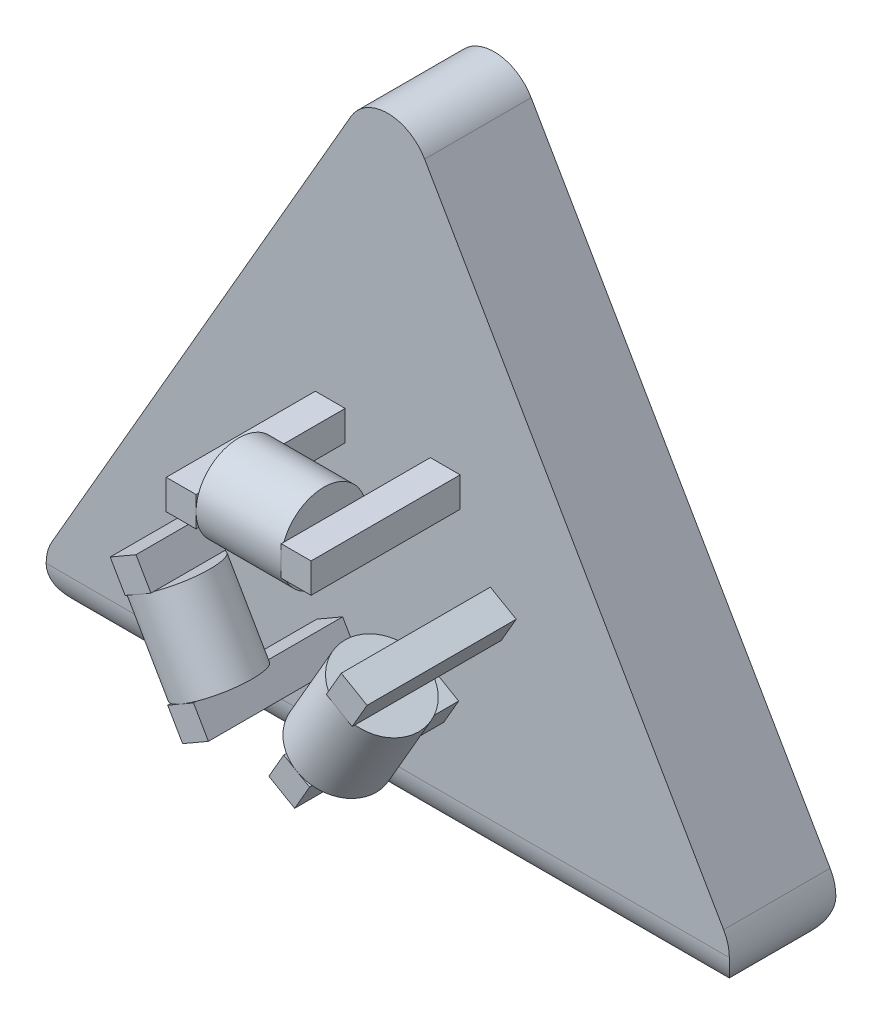
SolidWorks part; units mm, degrees
ref_plane "前视基准面" through (0, 0, 0) normal (0, 0, 1) x (1, 0, 0)
ref_plane "上视基准面" through (0, 0, 0) normal (0, 1, 0) x (1, 0, 0)
ref_plane "右视基准面" through (0, 0, 0) normal (1, 0, 0) x (0, 0, -1)
sketch "草图1" plane through (0, 0, 0) normal (0, 0, 1) x (1, 0, 0)
  line L0 (0, 0) -> (0, 40)
  line L1 (0, 40) -> (35, -20.6218)
  line L2 (0, 40) -> (-35, -20.6218)
  line L3 (-35, -20.6218) -> (35, -20.6218)
extrude "凸台-拉伸1" add sketch "草图1" along normal blind 10
fillet "圆角1" radius 4 5 edges at (0, -20.6218, 10) (0, -20.6218, 0) (35, -20.6218, 5) (-35, -20.6218, 5) (0, 40, 5)
sketch "草图2" plane through (0, 0, 10) normal (0, 0, 1) x (1, 0, 0)
  line L0 (0, 0) -> (0, 10)
  line L1 (0, 10) -> (4, 10)
  line L2 (0, 10) -> (-4, 10)
  line L3 (4, 10) -> (6.8, 10)
  line L4 (4, 10) -> (4, 7.2)
  line L5 (4, 7.2) -> (6.8, 7.2)
  line L6 (6.8, 10) -> (6.8, 7.2)
  line L7 (0, 0) -> (-8.6603, -5)
  line L8 (-4, 10) -> (-6.8, 10)
  line L9 (-4, 10) -> (-4, 7.2)
  line L10 (-4, 7.2) -> (-6.8, 7.2)
  line L11 (-6.8, 10) -> (-6.8, 7.2)
  line L12 (-8.6603, -5) -> (-10.6603, -1.5359)
  line L13 (-8.6603, -5) -> (-6.6603, -8.4641)
  line L14 (-10.6603, -1.5359) -> (-12.0603, 0.889)
  line L15 (-10.6603, -1.5359) -> (-8.2354, -0.1359)
  line L16 (-8.2354, -0.1359) -> (-9.6354, 2.289)
  line L17 (-12.0603, 0.889) -> (-9.6354, 2.289)
  line L18 (-6.6603, -8.4641) -> (-5.2603, -10.889)
  line L19 (-6.6603, -8.4641) -> (-4.2354, -7.0641)
  line L20 (-4.2354, -7.0641) -> (-2.8354, -9.489)
  line L21 (-5.2603, -10.889) -> (-2.8354, -9.489)
  line L22 (0, 0) -> (8.6603, -5)
  line L23 (8.6603, -5) -> (6.6603, -8.4641)
  line L24 (8.6603, -5) -> (10.6603, -1.5359)
  line L25 (6.6603, -8.4641) -> (5.2603, -10.889)
  line L26 (6.6603, -8.4641) -> (4.2354, -7.0641)
  line L27 (4.2354, -7.0641) -> (2.8354, -9.489)
  line L28 (5.2603, -10.889) -> (2.8354, -9.489)
  line L29 (10.6603, -1.5359) -> (12.0603, 0.889)
  line L30 (10.6603, -1.5359) -> (8.2354, -0.1359)
  line L31 (8.2354, -0.1359) -> (9.6354, 2.289)
  line L32 (12.0603, 0.889) -> (9.6354, 2.289)
extrude "凸台-拉伸2" add sketch "草图2" along normal blind 14 contours L8 L11 L10 L9 | L6 L3 L4 L5 | L29 L32 L31 L30 | L28 L25 L26 L27 | L18 L21 L20 L19 | L17 L14 L15 L16
sketch "草图3" plane through (-2, 3.4641, 0) normal (0.5, -0.866, 0) x (-0.866, -0.5, 0)
  line L0 (8.6, -24) -> (8.6, -20.4)
  line L1 (10, -24) -> (7.2, -24) construction
  circle A0 centre (8.6, -20.4) radius 3.6
extrude "凸台-拉伸3" add sketch "草图3" along normal blind 8
sketch "草图4" plane through (-4, 0, 0) normal (1, 0, 0) x (0, 0, -1)
  line L0 (-24, 8.6) -> (-20, 8.6)
  line L1 (-24, 10) -> (-24, 7.2) construction
  circle A0 centre (-20, 8.6) radius 4
extrude "凸台-拉伸4" add sketch "草图4" along normal blind 8
sketch "草图5" plane through (2, 3.4641, 0) normal (-0.5, -0.866, 0) x (-0.866, 0.5, 0)
  line L0 (-8.6, -24) -> (-8.6, -20)
  line L1 (-10, -24) -> (-7.2, -24) construction
  circle A0 centre (-8.6, -20) radius 4
extrude "凸台-拉伸5" add sketch "草图5" along normal blind 8
sketch "草图6" plane through (0, 0, 0) normal (0, 0, -1) x (-1, 0, 0)
  line L0 (0, 0) -> (0, -2)
  line L1 (0, -2) -> (0, 10)
  line L2 (-10, -3) -> (10, -3)
  line L3 (-10, -3) -> (-10, -1)
  line L4 (-10, -1) -> (10, -1)
  line L5 (10, -3) -> (10, -1)
  line L6 (-10, -3) -> (10, -1) construction
  line L7 (-10, -1) -> (10, -3) construction
  line L8 (0, 10) -> (7.5, 10)
  line L9 (0, 10) -> (-7.5, 10)
  circle A0 centre (7.5, 10) radius 2
  circle A1 centre (-7.5, 10) radius 2
extrude "切除-拉伸1" cut sketch "草图6" against normal blind 8
hole_wizard "M4 螺纹孔1" positions "草图11" profile "草图10" tap size "M4" standard "GB"
sketch "草图11" plane through (0, 0, 0) normal (0, 0, -1) x (-1, 0, 0)
  point P0 (-7.4974, 10.0202)
  point P2 (7.5604, 10.0202)
sketch "草图10" plane through (7.4974, 10.0202, 0) normal (1, 0, 0) x (0, 1, 0)
  line L0 (0, 0) -> (0, 5.9914)
  line L1 (0, 5.9914) -> (1.65, 5)
  line L2 (1.65, 5) -> (1.65, 0)
  line L5 (1.65, 0) -> (0, 0)
  line L10 (0, 5.9914) -> (-1.65, 5) construction
  line L11 (0, -6.35) -> (0, 107.95) construction
  dimension "螺纹孔钻头直径" = 3.3
  dimension "螺纹孔钻头深度" = 5
  dimension "导头角度" = 118
cosmetic thread "孔螺蚊线1" parameters "D1"=8, "D2"=4
cosmetic thread "孔螺蚊线2" parameters "D1"=8, "D2"=4
